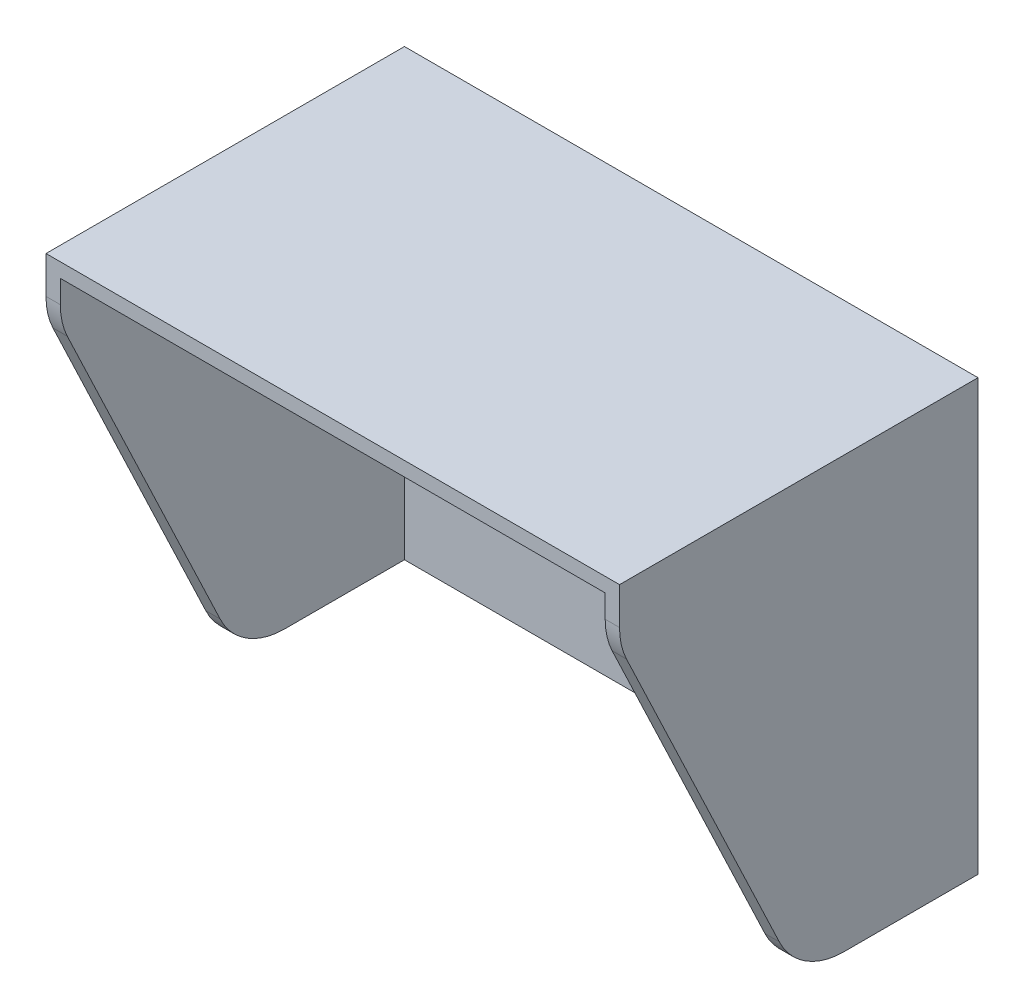
SolidWorks part; units mm, degrees
ref_plane "前视基准面" through (0, 0, 0) normal (0, 0, 1) x (1, 0, 0)
ref_plane "上视基准面" through (0, 0, 0) normal (0, 1, 0) x (1, 0, 0)
ref_plane "右视基准面" through (0, 0, 0) normal (1, 0, 0) x (0, 0, -1)
other "Configuration Table"
sketch "草图1" plane through (0, 0, 0) normal (0, 0, 1) x (1, 0, 0)
  line L0 (-8.9935, -21.6962) -> (-8.9935, 38.3038) construction
  line L1 (-48.9935, 38.3038) -> (31.0065, 38.3038)
  line L2 (-48.9935, 38.3038) -> (-48.9935, -21.6962)
  line L3 (-48.9935, -21.6962) -> (31.0065, -21.6962)
  line L4 (31.0065, 38.3038) -> (31.0065, -21.6962)
  line L5 (31.0065, -1.6962) -> (-8.9935, -1.6962) construction
  line L6 (11.0065, -1.6962) -> (11.0065, -21.6962) construction
  circle A0 centre (3.5065, -1.6962) radius 1.6
  circle A1 centre (18.5065, -1.6962) radius 1.6
  dimension "D3" = 7.5
  dimension "D5" = 3.2
  dimension "D1" = 80
  dimension "D2" = 60
  dimension "D4" = 7.5
  dimension "D6" = 20
extrude "凸台-拉伸1" add sketch "草图1" along normal blind 50
sketch "草图2" plane through (0, 0, 50) normal (0, 0, 1) x (1, 0, 0)
  line L0 (-48.9935, -21.6962) -> (31.0065, -21.6962) construction
  line L1 (-46.9935, -21.6962) -> (29.0065, -21.6962)
  line L2 (-46.9935, -21.6962) -> (-46.9935, 36.3038)
  line L3 (-46.9935, 36.3038) -> (29.0065, 36.3038)
  line L4 (29.0065, -21.6962) -> (29.0065, 36.3038)
  line L5 (31.0065, -21.6962) -> (31.0065, 38.3038) construction
  line L6 (-48.9935, 38.3038) -> (-48.9935, -21.6962) construction
  line L7 (31.0065, 38.3038) -> (-48.9935, 38.3038) construction
  dimension "D1" = 2
  dimension "D2" = 2
  dimension "D3" = 2
extrude "切除-拉伸1" cut sketch "草图2" against normal blind 48
sketch "草图3" plane through (-48.9935, 0, 0) normal (-1, 0, 0) x (0, 0, 1)
  line L0 (50, 30.8642) -> (25, -21.6962)
  line L1 (50, 38.3038) -> (50, -21.6962) construction
  line L2 (50, -21.6962) -> (0, -21.6962) construction
  line L3 (25, -21.6962) -> (50, -21.6962)
  line L4 (50, -21.6962) -> (50, 30.8642)
  point P6 (0, 0)
extrude "切除-拉伸2" cut sketch "草图3" against normal through all
fillet "圆角1" radius 10 4 edges at (30.0065, 30.8642, 50) (-47.9935, 30.8642, 50) (30.0065, -21.6962, 25) (-47.9935, -21.6962, 25)
